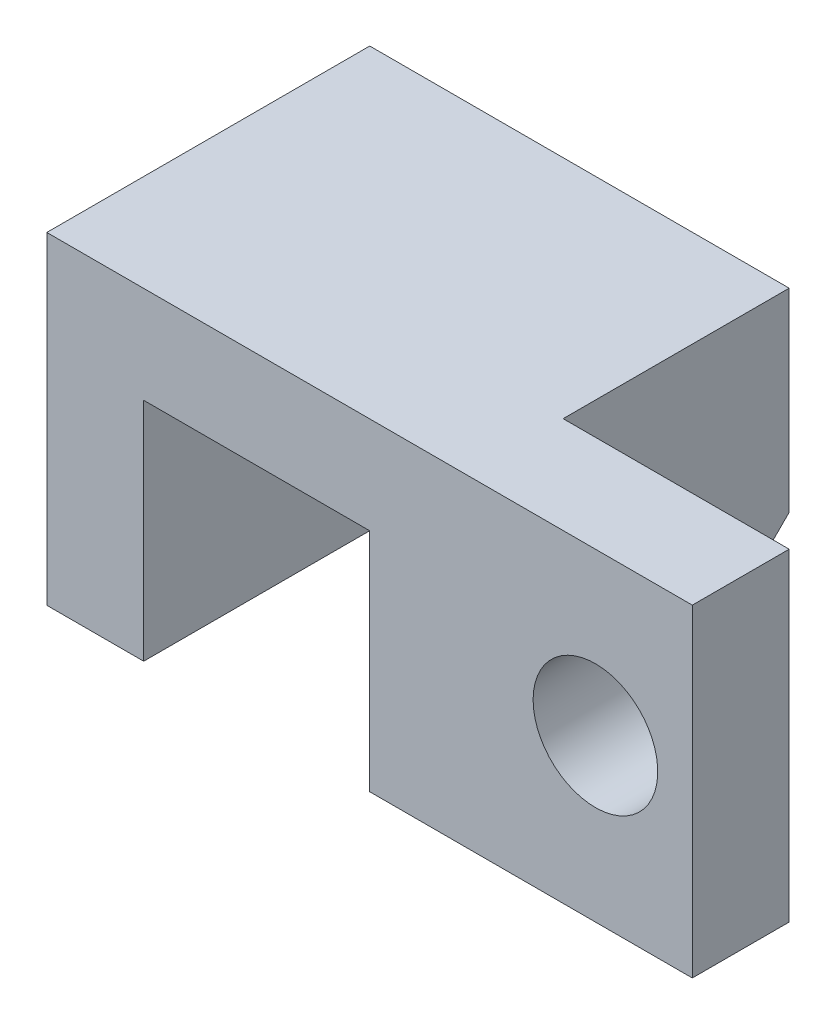
SolidWorks part; units mm, degrees
ref_plane "Front Plane" through (0, 0, 0) normal (0, 0, 1) x (1, 0, 0)
ref_plane "Top Plane" through (0, 0, 0) normal (0, 1, 0) x (1, 0, 0)
ref_plane "Right Plane" through (0, 0, 0) normal (1, 0, 0) x (0, 0, -1)
sketch "Sketch3" plane through (0, 0, 0) normal (0, 1, 0) x (1, 0, 0)
  line L0 (-130.7545, 4.6721) -> (-130.7545, -58.8279)
  line L1 (-130.7545, -58.8279) -> (-67.2545, -58.8279)
  line L2 (-67.2545, -58.8279) -> (-67.2545, -39.7779)
  line L3 (-67.2545, -39.7779) -> (-111.7045, -39.7779)
  line L4 (-111.7045, -39.7779) -> (-111.7045, 4.6721)
  line L5 (-111.7045, 4.6721) -> (-130.7545, 4.6721)
extrude "Boss-Extrude1" add sketch "Sketch3" along normal blind 63.5
sketch "Sketch4" plane through (0, 0, -4.6721) normal (0, 0, -1) x (-1, 0, 0)
  line L0 (130.7545, 63.5) -> (130.7545, 44.4434)
  line L1 (130.7545, 63.5) -> (130.7545, 0) construction
  line L2 (130.7545, 44.4434) -> (175.1355, 44.4434)
  line L3 (175.1355, 44.4434) -> (175.1355, 0)
  line L4 (175.1355, 0) -> (194.1835, 0)
  line L5 (194.1835, 0) -> (194.1835, 63.5)
  line L6 (194.1835, 63.5) -> (130.7545, 63.5)
extrude "Boss-Extrude2" add sketch "Sketch4" against normal blind 63.5
sketch "Sketch5" plane through (0, 0, 39.7779) normal (0, 0, -1) x (-1, 0, 0)
  circle A0 centre (88.8102, 31.75) radius 12.0661
sketch "Sketch6" plane through (0, 0, 39.7779) normal (0, 0, -1) x (-1, 0, 0)
  line L0 (67.2545, 63.5) -> (111.7045, 63.5) construction
  line L1 (67.2545, 63.5) -> (67.2545, 0) construction
  circle A0 centre (86.3045, 31.75) radius 12.2542
  point P8 (67.2545, 31.75)
  dimension "D1" = 31.75
  dimension "D2" = 19.05
extrude "Cut-Extrude1" cut sketch "Sketch6" against normal through all
sketch "Sketch7" plane through (-111.7045, 0, 0) normal (1, 0, 0) x (0, 0, -1)
  line L0 (-13.7233, 0) -> (4.6721, 18.3954)
  line L1 (-39.7779, 0) -> (4.6721, 0) construction
  line L2 (4.6721, 63.5) -> (4.6721, 0) construction
sketch "Sketch8" plane through (-111.7045, 0, 0) normal (1, 0, 0) x (0, 0, -1)
  line L0 (4.6721, 0) -> (4.6721, 25.3262)
  line L1 (4.6721, 63.5) -> (4.6721, 0) construction
  line L2 (4.6721, 25.3262) -> (-20.6541, 0)
  line L3 (-39.7779, 0) -> (4.6721, 0) construction
  line L4 (-20.6541, 0) -> (4.6721, 0)
extrude "Cut-Extrude2" cut sketch "Sketch8" against normal blind 19.05
